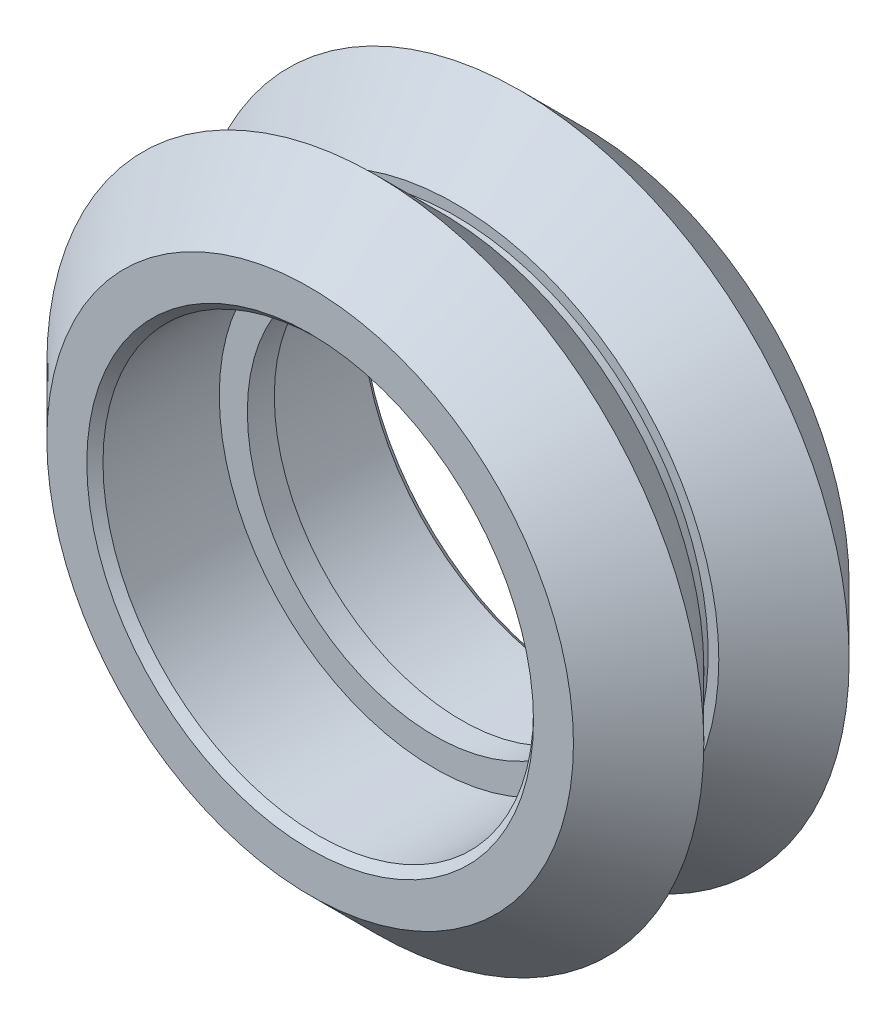
SolidWorks part; units mm, degrees
ref_plane "Front Plane" through (0, 0, 0) normal (0, 0, 1) x (1, 0, 0)
ref_plane "Top Plane" through (0, 0, 0) normal (0, 1, 0) x (1, 0, 0)
ref_plane "Right Plane" through (0, 0, 0) normal (1, 0, 0) x (0, 0, -1)
sketch "Sketch1" plane through (0, 0, 0) normal (0, 1, 0) x (1, 0, 0)
  line L0 (0, 5.115) -> (0, -5.115) construction
  line L1 (0, 5.115) -> (-9.77, 5.115)
  line L2 (-9.77, 5.115) -> (-12.1883, 2.6967)
  line L3 (-12.1883, 2.6967) -> (-9.77, 0.2784)
  line L4 (-9.77, -0.2784) -> (-12.1883, -2.6967)
  line L5 (-12.1883, -2.6967) -> (-9.77, -5.115)
  line L6 (-9.77, -5.115) -> (0, -5.115)
  line L7 (-9.77, 0.2784) -> (-9.375, 0.2784)
  line L8 (-9.375, 0.2784) -> (-9.375, -0.2784)
  line L9 (-9.375, -0.2784) -> (-9.77, -0.2784)
  line L10 (-7.987, 5.115) -> (-7.987, 0.5)
  line L11 (-7.987, 0.5) -> (-6.945, 0.5)
  line L12 (-6.945, 0.5) -> (-6.945, -0.5)
  line L13 (-6.945, -0.5) -> (-7.987, -0.5)
  line L14 (-7.987, -0.5) -> (-7.987, -5.115)
  dimension "D2" = 9.375
  dimension "D3" = 12.1883
  dimension "D4" = 6.945
  dimension "D5" = 10.23
  dimension "D6" = 9.77
  dimension "D7" = 3.42
  dimension "D8" = 5.3934
  dimension "D9" = 7.987
  dimension "D10" = 90
  dimension "D11" = 1
revolve "Revolve1" add sketch "Sketch1" angle 360 about L0
chamfer "Chamfer1" distance 0.3 angle 45 2 edges at (-7.987, 0, 5.115) (-7.987, 0, -5.115)
